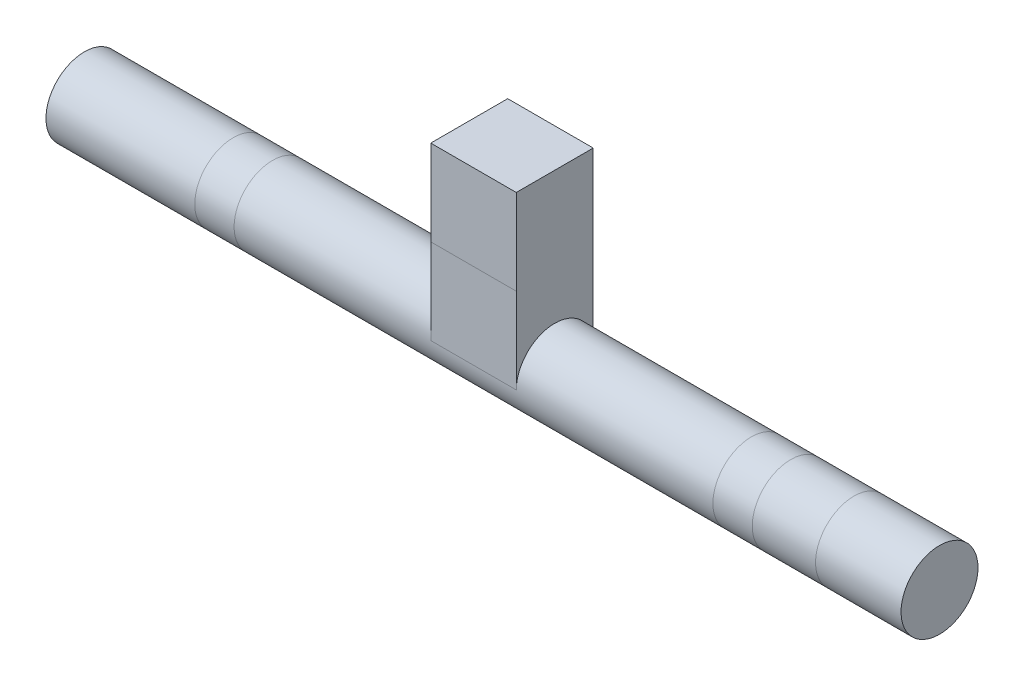
SolidWorks part; units mm, degrees
material "1.0037 (S235JR)"
ref_plane "Plan de face" through (0, 0, 0) normal (0, 0, 1) x (1, 0, 0)
ref_plane "Plan de dessus" through (0, 0, 0) normal (0, 1, 0) x (1, 0, 0)
ref_plane "Plan de droite" through (0, 0, 0) normal (1, 0, 0) x (0, 0, -1)
sketch "Esquisse1" plane through (0, 0, 0) normal (1, 0, 0) x (0, 0, -1)
  circle A0 centre (0, 0) radius 45
  dimension "D1" = 90
extrude "Boss.-Extru.1" add sketch "Esquisse1" along normal mid plane 1000
sketch "Esquisse2" plane through (0, 0, 0) normal (1, 0, 0) x (0, 0, -1)
  line L4 (-45, 200) -> (45, 200)
  line L5 (-45, 200) -> (-45, 0)
  line L6 (-45, 0) -> (45, 0)
  line L7 (45, 200) -> (45, 0)
  circle A2 centre (0, 0) radius 45 construction
  dimension "D1" = 200
extrude "Boss.-Extru.2" add sketch "Esquisse2" along normal mid plane 100
sketch "Esquisse3" plane through (0, 0, 0) normal (0, 0, 1) x (1, 0, 0)
  line L0 (-326, 45) -> (-326, -45)
  line L1 (-50, 45) -> (-500, 45) construction
  line L2 (-500, -45) -> (500, -45) construction
  line L4 (-280, 45) -> (-280, -45)
  line L5 (400, 45) -> (400, -45)
  line L6 (500, 45) -> (50, 45) construction
  line L7 (280, 45) -> (280, -45)
  line L8 (500, -45) -> (500, 45) construction
  line L9 (326, 45) -> (326, -45)
  dimension "D1" = 280
  dimension "D2" = 280
  dimension "D3" = 46
  dimension "D4" = 46
  dimension "D5" = 100
split line "Ligne de séparation1"
sketch "Esquisse5" plane through (0, 0, 0) normal (0, 0, 1) x (1, 0, 0)
  line L0 (-50, 100) -> (50, 100)
  line L1 (-50, 200) -> (-50, 0) construction
  line L2 (50, 200) -> (50, 0) construction
  line L3 (0, 200) -> (0, 100) construction
  line L4 (50, 200) -> (-50, 200) construction
  point P10 (0, 150)
  dimension "D1" = 150
split line "Ligne de séparation2"
